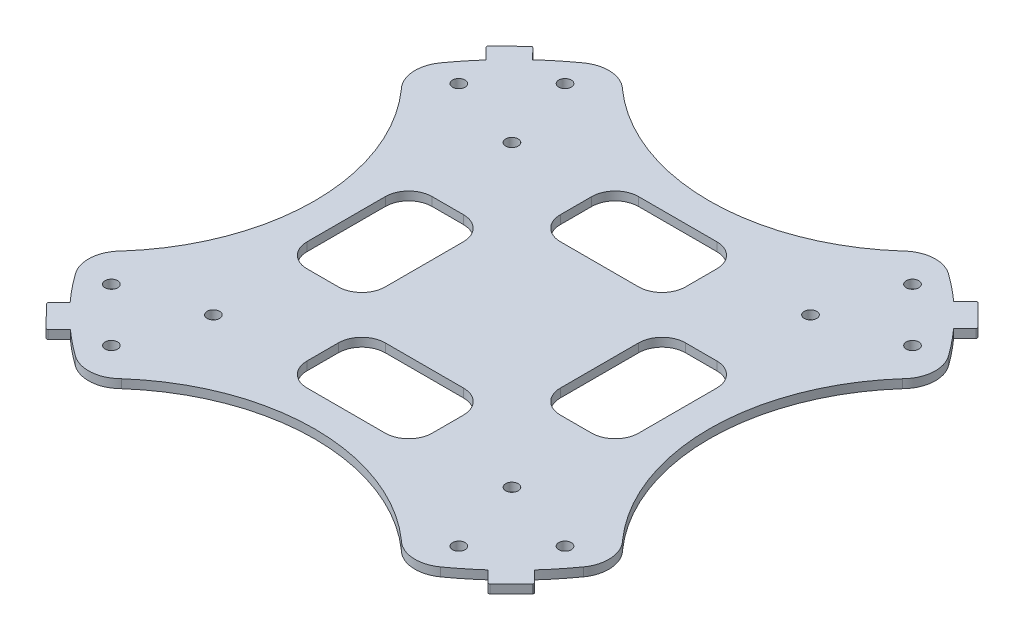
SolidWorks part; units mm, degrees
ref_plane "Front Plane" through (0, 0, 0) normal (0, 0, 1) x (1, 0, 0)
ref_plane "Top Plane" through (0, 0, 0) normal (0, 1, 0) x (1, 0, 0)
ref_plane "Right Plane" through (0, 0, 0) normal (1, 0, 0) x (0, 0, -1)
sketch "Sketch1" plane through (0, 0, 0) normal (0, 1, 0) x (1, 0, 0)
  line L0 (-1000, 0) -> (49000, 0) construction
  line L1 (0, -1000) -> (0, 49000) construction
  line L2 (707.1069, -707.1069) -> (-34648.2322, 34648.2322) construction
  line L3 (-707.1068, -707.1068) -> (34648.2323, 34648.2323) construction
  line L4 (716.0871, -698.1266) -> (0, 17.9605) construction
  line L5 (-698.1265, -716.087) -> (34657.2125, 34639.252) construction
  line L6 (698.1266, -716.0871) -> (-34657.2125, 34639.2519) construction
  line L7 (-716.087, -698.1265) -> (0, 17.9605) construction
  line L8 (-733.6258, -670.2104) -> (-31.7077, 31.7077) construction
  line L9 (733.9751, -670.5597) -> (22.7274, 40.6879) construction
  line L10 (39.5829, 36.115) -> (36.1358, 39.5583)
  line L11 (716.0871, -698.1266) -> (-34639.2519, 34657.2125) construction
  line L12 (35.7817, 39.5534) -> (33.9856, 37.7573)
  line L13 (-716.087, -698.1265) -> (34639.252, 34657.2125) construction
  line L14 (39.5739, 35.7609) -> (37.7573, 33.9856)
  line L15 (39.5382, -36.1548) -> (36.0819, -39.6111)
  line L16 (39.5078, -35.8322) -> (37.7118, -34.0362)
  line L17 (-35.9968, -39.6764) -> (-39.3444, -36.2512)
  line L18 (-37.6038, -34.1555) -> (-39.3423, -35.894)
  line L19 (35.7129, -39.6171) -> (33.9376, -37.8006)
  line L20 (-35.6141, -39.7036) -> (-33.8181, -37.9075)
  line L21 (-39.7221, 35.8999) -> (-36.251, 39.2922)
  line L22 (-34.2033, 37.5603) -> (-35.8918, 39.2881)
  line L24 (-37.9528, 33.7672) -> (-39.7242, 35.5386)
  line L30 (-39.4203, -35.9308) -> (-37.6038, -34.1555) [skipped]
  line L31 (-39.7488, 35.5633) -> (-37.9528, 33.7672) [skipped]
  line L32 (-35.9786, 39.3768) -> (-34.2033, 37.5603) [skipped]
  arc A0 (-29.6486, 41.2505) -> (-34.2033, 37.5603) centre (0, 0) ccw construction
  arc A1 (-22.7274, 40.6879) -> (-29.6486, 41.2505) centre (-26.519, 36.8963) ccw
  arc A2 (-40.6879, 22.7274) -> (-41.2505, 29.6486) centre (-36.8963, 26.519) cw
  arc A3 (22.7274, 40.6879) -> (29.6486, 41.2505) centre (26.519, 36.8963) cw
  arc A4 (40.6879, 22.7274) -> (41.2505, 29.6486) centre (36.8963, 26.519) ccw
  arc A5 (40.6879, -22.7274) -> (41.2505, -29.6486) centre (36.8963, -26.519) cw
  arc A6 (22.7274, -40.6879) -> (29.6486, -41.2505) centre (26.519, -36.8963) ccw
  arc A7 (-22.7274, -40.6879) -> (-29.6486, -41.2505) centre (-26.519, -36.8963) cw
  arc A8 (-40.6879, -22.7274) -> (-41.2505, -29.6486) centre (-36.8963, -26.519) ccw
  arc A9 (-22.7274, 40.6879) -> (22.7274, 40.6879) centre (0, 66.2866) ccw
  arc A10 (40.6879, 22.7274) -> (40.6879, -22.7274) centre (66.2866, 0) ccw
  arc A11 (22.7274, -40.6879) -> (-22.7274, -40.6879) centre (0, -66.2866) ccw
  arc A12 (-40.6879, -22.7274) -> (-40.6879, 22.7274) centre (-66.2866, 0) ccw
  arc A13 (-29.6486, 41.2505) -> (-34.2033, 37.5603) centre (0, 0) ccw
  arc A14 (41.2505, 29.6486) -> (37.7573, 33.9856) centre (0, 0) ccw construction
  arc A15 (41.2505, 29.6486) -> (37.7573, 33.9856) centre (0, 0) ccw
  arc A16 (29.6486, -41.2505) -> (33.9376, -37.8006) centre (0, 0) ccw construction
  arc A17 (29.6486, -41.2505) -> (33.9376, -37.8006) centre (0, 0) ccw
  arc A18 (-41.2505, -29.6486) -> (-37.6038, -34.1555) centre (0, 0) ccw construction
  arc A19 (-41.2505, -29.6486) -> (-37.6038, -34.1555) centre (0, 0) ccw
  arc A20 (33.9856, 37.7573) -> (29.6486, 41.2505) centre (0, 0) ccw construction
  arc A21 (33.9856, 37.7573) -> (29.6486, 41.2505) centre (0, 0) ccw
  arc A22 (37.7118, -34.0362) -> (41.2505, -29.6486) centre (0, 0) ccw construction
  arc A23 (37.7118, -34.0362) -> (41.2505, -29.6486) centre (0, 0) ccw
  arc A24 (-33.8181, -37.9075) -> (-29.6486, -41.2505) centre (0, 0) ccw construction
  arc A25 (-33.8181, -37.9075) -> (-29.6486, -41.2505) centre (0, 0) ccw
  arc A26 (-37.9528, 33.7672) -> (-41.2505, 29.6486) centre (0, 0) ccw construction
  arc A27 (-37.9528, 33.7672) -> (-41.2505, 29.6486) centre (0, 0) ccw
  arc A28 (-35.6141, -39.7036) -> (-35.9968, -39.6764) centre (-35.7937, -39.5239) cw
  arc A29 (-39.3423, -35.894) -> (-39.3444, -36.2512) centre (-39.1627, -36.0736) ccw
  arc A30 (35.7129, -39.6171) -> (36.0819, -39.6111) centre (35.8945, -39.4396) ccw
  arc A31 (39.5078, -35.8322) -> (39.5382, -36.1548) centre (39.3282, -36.0118) cw
  arc A32 (39.5739, 35.7609) -> (39.5829, 36.115) centre (39.3964, 35.9426) ccw
  arc A33 (36.1358, 39.5583) -> (35.7817, 39.5534) centre (35.9613, 39.3738) ccw
  arc A34 (-39.7221, 35.8999) -> (-39.7242, 35.5386) centre (-39.5446, 35.7182) ccw
  arc A35 (-36.251, 39.2922) -> (-35.8918, 39.2881) centre (-36.0735, 39.1105) cw
  circle A36 centre (-28.2202, 36.8412) radius 1.016
  circle A37 centre (-36.8412, 28.2202) radius 1.016
  circle A38 centre (-24.2455, 24.2455) radius 1.016
  circle A39 centre (28.2202, 36.8412) radius 1.016
  circle A40 centre (36.8412, 28.2202) radius 1.016
  circle A41 centre (24.2455, 24.2455) radius 1.016
  circle A42 centre (36.8412, -28.2202) radius 1.016
  circle A43 centre (28.2202, -36.8412) radius 1.016
  circle A44 centre (24.2455, -24.2455) radius 1.016
  circle A45 centre (-28.2202, -36.8412) radius 1.016
  circle A46 centre (-36.8412, -28.2202) radius 1.016
  circle A47 centre (-24.2455, -24.2455) radius 1.016
  point P46 (0, 0)
  point P60 (0, 0)
  point P75 (-0.048, -0.2069)
  point P83 (41.6473, 37.8756)
  point P86 (37.8756, 41.6473)
  point P120 (0, 0)
  dimension "D1" = 12.7
  dimension "D3" = 4
  dimension "D4" = 4
  dimension "D7" = 0.254
  dimension "D8" = 50.8
  dimension "D10" = 0.254
  dimension "D9" = 0.254
  dimension "D13" = 13.208
  dimension "D5" = 2.667
  dimension "D11" = 12.192
  dimension "D12" = 7.366
  dimension "D2" = 12.7
  dimension "D6" = 4
  dimension "D14" = 4
extrude "Boss-Extrude1" add sketch "Sketch1" along normal blind 1.397
sketch "Sketch3" plane through (0, 1.397, 0) normal (0, 1, 0) x (1, 0, 0)
  line L0 (0, 0) -> (0, 50000) construction
  line L1 (26.924, 6.35) -> (26.924, -6.35)
  line L2 (-6.35, 26.924) -> (6.35, 26.924)
  line L3 (-10.16, 23.114) -> (-10.16, 18.034)
  line L4 (-6.35, 14.224) -> (6.35, 14.224)
  line L5 (10.16, 23.114) -> (10.16, 18.034)
  line L6 (-10.16, 26.924) -> (10.16, 14.224) construction
  line L7 (-10.16, 14.224) -> (10.16, 26.924) construction
  line L8 (23.114, -10.16) -> (18.034, -10.16)
  line L9 (14.224, 6.35) -> (14.224, -6.35)
  line L10 (23.114, 10.16) -> (18.034, 10.16)
  line L11 (6.35, -26.924) -> (-6.35, -26.924)
  line L12 (-10.16, -23.114) -> (-10.16, -18.034)
  line L13 (6.35, -14.224) -> (-6.35, -14.224)
  line L14 (10.16, -23.114) -> (10.16, -18.034)
  line L15 (-26.924, -6.35) -> (-26.924, 6.35)
  line L16 (-23.114, 10.16) -> (-18.034, 10.16)
  line L17 (-14.224, -6.35) -> (-14.224, 6.35)
  line L18 (-23.114, -10.16) -> (-18.034, -10.16)
  arc A0 (-10.16, 23.114) -> (-6.35, 26.924) centre (-6.35, 23.114) cw
  arc A1 (-10.16, 18.034) -> (-6.35, 14.224) centre (-6.35, 18.034) ccw
  arc A2 (10.16, 18.034) -> (6.35, 14.224) centre (6.35, 18.034) cw
  arc A3 (10.16, 23.114) -> (6.35, 26.924) centre (6.35, 23.114) ccw
  arc A4 (23.114, 10.16) -> (26.924, 6.35) centre (23.114, 6.35) cw
  arc A5 (23.114, -10.16) -> (26.924, -6.35) centre (23.114, -6.35) ccw
  arc A6 (18.034, 10.16) -> (14.224, 6.35) centre (18.034, 6.35) ccw
  arc A7 (18.034, -10.16) -> (14.224, -6.35) centre (18.034, -6.35) cw
  arc A8 (10.16, -23.114) -> (6.35, -26.924) centre (6.35, -23.114) cw
  arc A9 (-10.16, -23.114) -> (-6.35, -26.924) centre (-6.35, -23.114) ccw
  arc A10 (10.16, -18.034) -> (6.35, -14.224) centre (6.35, -18.034) ccw
  arc A11 (-10.16, -18.034) -> (-6.35, -14.224) centre (-6.35, -18.034) cw
  arc A12 (-23.114, -10.16) -> (-26.924, -6.35) centre (-23.114, -6.35) cw
  arc A13 (-23.114, 10.16) -> (-26.924, 6.35) centre (-23.114, 6.35) ccw
  arc A14 (-18.034, -10.16) -> (-14.224, -6.35) centre (-18.034, -6.35) ccw
  arc A15 (-18.034, 10.16) -> (-14.224, 6.35) centre (-18.034, 6.35) cw
  point P3 (0, 20.574)
  point P59 (0, 0)
  dimension "D3" = 26.924
  dimension "D4" = 3.81
  dimension "D1" = 12.7
  dimension "D2" = 20.32
  dimension "D5" = 4
extrude "Cut-Extrude1" cut sketch "Sketch3" against normal blind 1.397
sketch "Sketch4" plane through (0, 0, 0) normal (0, -1, 0) x (1, 0, 0)
  line L24 (34.0319, -34.9752) -> (35.9619, -36.9052)
  line L25 (35.9619, -36.9052) -> (36.9121, -35.956)
  line L26 (36.9121, -35.956) -> (34.9596, -34.048)
  line L27 (34.9278, 34.0806) -> (36.8559, 36.0087)
  line L28 (36.8559, 36.0087) -> (35.9086, 36.9559)
  line L29 (35.9086, 36.9559) -> (34.0017, 35.0047)
  line L30 (-33.8705, 35.1316) -> (-35.778, 37.039)
  line L31 (-35.778, 37.039) -> (-36.7076, 36.0877)
  line L32 (-36.7076, 36.0877) -> (-34.8154, 34.1955)
  line L33 (-35.1787, -33.8216) -> (-37.0611, -35.704)
  line L34 (-37.0611, -35.704) -> (-36.1018, -36.6415)
  line L35 (-36.1018, -36.6415) -> (-34.2575, -34.7543)
  line L36 (34.0319, -34.9752) -> (35.9619, -36.9052)
  line L37 (35.9619, -36.9052) -> (36.9121, -35.956)
  line L38 (36.9121, -35.956) -> (34.9596, -34.048)
  line L39 (34.9278, 34.0806) -> (36.8559, 36.0087)
  line L40 (36.8559, 36.0087) -> (35.9086, 36.9559)
  line L41 (35.9086, 36.9559) -> (34.0017, 35.0047)
  line L42 (-33.8705, 35.1316) -> (-35.778, 37.039)
  line L43 (-35.778, 37.039) -> (-36.7076, 36.0877)
  line L44 (-36.7076, 36.0877) -> (-34.8154, 34.1955)
  line L45 (-35.1787, -33.8216) -> (-37.0611, -35.704)
  line L46 (-37.0611, -35.704) -> (-36.1018, -36.6415)
  line L47 (-36.1018, -36.6415) -> (-34.2575, -34.7543)
  line L60 (33.9856, -37.7573) -> (35.7817, -39.5534)
  line L61 (36.1358, -39.5583) -> (39.5829, -36.115)
  line L62 (39.5739, -35.7609) -> (37.7573, -33.9856)
  line L63 (37.7118, 34.0362) -> (39.5078, 35.8322)
  line L64 (39.5382, 36.1548) -> (36.0819, 39.6111)
  line L65 (35.7129, 39.6171) -> (33.9376, 37.8006)
  line L66 (-33.8181, 37.9075) -> (-35.6141, 39.7036)
  line L67 (-35.9968, 39.6764) -> (-39.3444, 36.2512)
  line L68 (-39.3423, 35.894) -> (-37.6038, 34.1555)
  line L69 (-37.9528, -33.7672) -> (-39.7242, -35.5386)
  line L70 (-39.7221, -35.8999) -> (-36.251, -39.2922)
  line L71 (-35.8918, -39.2881) -> (-34.2033, -37.5603)
  line L72 (33.9856, -37.7573) -> (35.7817, -39.5534)
  line L73 (36.1358, -39.5583) -> (39.5829, -36.115)
  line L74 (39.5739, -35.7609) -> (37.7573, -33.9856)
  line L75 (37.7118, 34.0362) -> (39.5078, 35.8322)
  line L76 (39.5382, 36.1548) -> (36.0819, 39.6111)
  line L77 (35.7129, 39.6171) -> (33.9376, 37.8006)
  line L78 (-33.8181, 37.9075) -> (-35.6141, 39.7036)
  line L79 (-35.9968, 39.6764) -> (-39.3444, 36.2512)
  line L80 (-39.3423, 35.894) -> (-37.6038, 34.1555)
  line L81 (-37.9528, -33.7672) -> (-39.7242, -35.5386)
  line L82 (-39.7221, -35.8999) -> (-36.251, -39.2922)
  line L83 (-35.8918, -39.2881) -> (-34.2033, -37.5603)
  arc A56 (-34.2575, -34.7543) -> (-28.4813, -39.6265) centre (0, 0) ccw
  arc A57 (-28.4813, -39.6265) -> (-24.1054, -39.2369) centre (-26.519, -36.8963) ccw
  arc A58 (24.1054, -39.2369) -> (-24.1054, -39.2369) centre (0, -66.2866) ccw
  arc A59 (24.1054, -39.2369) -> (28.4813, -39.6265) centre (26.519, -36.8963) ccw
  arc A60 (28.4813, -39.6265) -> (34.0319, -34.9752) centre (0, 0) ccw
  arc A61 (34.9596, -34.048) -> (39.6265, -28.4813) centre (0, 0) ccw
  arc A62 (39.6265, -28.4813) -> (39.2369, -24.1054) centre (36.8963, -26.519) ccw
  arc A63 (39.2369, 24.1054) -> (39.2369, -24.1054) centre (66.2866, 0) ccw
  arc A64 (39.2369, 24.1054) -> (39.6265, 28.4813) centre (36.8963, 26.519) ccw
  arc A65 (39.6265, 28.4813) -> (34.9278, 34.0806) centre (0, 0) ccw
  arc A66 (34.0017, 35.0047) -> (28.4813, 39.6265) centre (0, 0) ccw
  arc A67 (28.4813, 39.6265) -> (24.1054, 39.2369) centre (26.519, 36.8963) ccw
  arc A68 (-24.1054, 39.2369) -> (24.1054, 39.2369) centre (0, 66.2866) ccw
  arc A69 (-24.1054, 39.2369) -> (-28.4813, 39.6265) centre (-26.519, 36.8963) ccw
  arc A70 (-28.4813, 39.6265) -> (-33.8705, 35.1316) centre (0, 0) ccw
  arc A71 (-34.8154, 34.1955) -> (-39.6265, 28.4813) centre (0, 0) ccw
  arc A72 (-39.6265, 28.4813) -> (-39.2369, 24.1054) centre (-36.8963, 26.519) ccw
  arc A73 (-39.2369, -24.1054) -> (-39.2369, 24.1054) centre (-66.2866, 0) ccw
  arc A74 (-39.2369, -24.1054) -> (-39.6265, -28.4813) centre (-36.8963, -26.519) ccw
  arc A75 (-39.6265, -28.4813) -> (-35.1787, -33.8216) centre (0, 0) ccw
  arc A76 (-34.2575, -34.7543) -> (-28.4813, -39.6265) centre (0, 0) ccw
  arc A77 (-28.4813, -39.6265) -> (-24.1054, -39.2369) centre (-26.519, -36.8963) ccw
  arc A78 (24.1054, -39.2369) -> (-24.1054, -39.2369) centre (0, -66.2866) ccw
  arc A79 (24.1054, -39.2369) -> (28.4813, -39.6265) centre (26.519, -36.8963) ccw
  arc A80 (28.4813, -39.6265) -> (34.0319, -34.9752) centre (0, 0) ccw
  arc A81 (34.9596, -34.048) -> (39.6265, -28.4813) centre (0, 0) ccw
  arc A82 (39.6265, -28.4813) -> (39.2369, -24.1054) centre (36.8963, -26.519) ccw
  arc A83 (39.2369, 24.1054) -> (39.2369, -24.1054) centre (66.2866, 0) ccw
  arc A84 (39.2369, 24.1054) -> (39.6265, 28.4813) centre (36.8963, 26.519) ccw
  arc A85 (39.6265, 28.4813) -> (34.9278, 34.0806) centre (0, 0) ccw
  arc A86 (34.0017, 35.0047) -> (28.4813, 39.6265) centre (0, 0) ccw
  arc A87 (28.4813, 39.6265) -> (24.1054, 39.2369) centre (26.519, 36.8963) ccw
  arc A88 (-24.1054, 39.2369) -> (24.1054, 39.2369) centre (0, 66.2866) ccw
  arc A89 (-24.1054, 39.2369) -> (-28.4813, 39.6265) centre (-26.519, 36.8963) ccw
  arc A90 (-28.4813, 39.6265) -> (-33.8705, 35.1316) centre (0, 0) ccw
  arc A91 (-34.8154, 34.1955) -> (-39.6265, 28.4813) centre (0, 0) ccw
  arc A92 (-39.6265, 28.4813) -> (-39.2369, 24.1054) centre (-36.8963, 26.519) ccw
  arc A93 (-39.2369, -24.1054) -> (-39.2369, 24.1054) centre (-66.2866, 0) ccw
  arc A94 (-39.2369, -24.1054) -> (-39.6265, -28.4813) centre (-36.8963, -26.519) ccw
  arc A95 (-39.6265, -28.4813) -> (-35.1787, -33.8216) centre (0, 0) ccw
  arc A124 (-34.2033, -37.5603) -> (-29.6486, -41.2505) centre (0, 0) ccw
  arc A125 (-29.6486, -41.2505) -> (-22.7274, -40.6879) centre (-26.519, -36.8963) ccw
  arc A126 (22.7274, -40.6879) -> (-22.7274, -40.6879) centre (0, -66.2866) ccw
  arc A127 (22.7274, -40.6879) -> (29.6486, -41.2505) centre (26.519, -36.8963) ccw
  arc A128 (29.6486, -41.2505) -> (33.9856, -37.7573) centre (0, 0) ccw
  arc A129 (35.7817, -39.5534) -> (36.1358, -39.5583) centre (35.9613, -39.3738) ccw
  arc A130 (39.5829, -36.115) -> (39.5739, -35.7609) centre (39.3964, -35.9426) ccw
  arc A131 (37.7573, -33.9856) -> (41.2505, -29.6486) centre (0, 0) ccw
  arc A132 (41.2505, -29.6486) -> (40.6879, -22.7274) centre (36.8963, -26.519) ccw
  arc A133 (40.6879, 22.7274) -> (40.6879, -22.7274) centre (66.2866, 0) ccw
  arc A134 (40.6879, 22.7274) -> (41.2505, 29.6486) centre (36.8963, 26.519) ccw
  arc A135 (41.2505, 29.6486) -> (37.7118, 34.0362) centre (0, 0) ccw
  arc A136 (39.5078, 35.8322) -> (39.5382, 36.1548) centre (39.3282, 36.0118) ccw
  arc A137 (36.0819, 39.6111) -> (35.7129, 39.6171) centre (35.8945, 39.4396) ccw
  arc A138 (33.9376, 37.8006) -> (29.6486, 41.2505) centre (0, 0) ccw
  arc A139 (29.6486, 41.2505) -> (22.7274, 40.6879) centre (26.519, 36.8963) ccw
  arc A140 (-22.7274, 40.6879) -> (22.7274, 40.6879) centre (0, 66.2866) ccw
  arc A141 (-22.7274, 40.6879) -> (-29.6486, 41.2505) centre (-26.519, 36.8963) ccw
  arc A142 (-29.6486, 41.2505) -> (-33.8181, 37.9075) centre (0, 0) ccw
  arc A143 (-35.6141, 39.7036) -> (-35.9968, 39.6764) centre (-35.7937, 39.5239) ccw
  arc A144 (-39.3444, 36.2512) -> (-39.3423, 35.894) centre (-39.1627, 36.0736) ccw
  arc A145 (-37.6038, 34.1555) -> (-41.2505, 29.6486) centre (0, 0) ccw
  arc A146 (-41.2505, 29.6486) -> (-40.6879, 22.7274) centre (-36.8963, 26.519) ccw
  arc A147 (-40.6879, -22.7274) -> (-40.6879, 22.7274) centre (-66.2866, 0) ccw
  arc A148 (-40.6879, -22.7274) -> (-41.2505, -29.6486) centre (-36.8963, -26.519) ccw
  arc A149 (-41.2505, -29.6486) -> (-37.9528, -33.7672) centre (0, 0) ccw
  arc A150 (-39.7242, -35.5386) -> (-39.7221, -35.8999) centre (-39.5446, -35.7182) ccw
  arc A151 (-36.251, -39.2922) -> (-35.8918, -39.2881) centre (-36.0735, -39.1105) ccw
  arc A152 (-34.2033, -37.5603) -> (-29.6486, -41.2505) centre (0, 0) ccw
  arc A153 (-29.6486, -41.2505) -> (-22.7274, -40.6879) centre (-26.519, -36.8963) ccw
  arc A154 (22.7274, -40.6879) -> (-22.7274, -40.6879) centre (0, -66.2866) ccw
  arc A155 (22.7274, -40.6879) -> (29.6486, -41.2505) centre (26.519, -36.8963) ccw
  arc A156 (29.6486, -41.2505) -> (33.9856, -37.7573) centre (0, 0) ccw
  arc A157 (35.7817, -39.5534) -> (36.1358, -39.5583) centre (35.9613, -39.3738) ccw
  arc A158 (39.5829, -36.115) -> (39.5739, -35.7609) centre (39.3964, -35.9426) ccw
  arc A159 (37.7573, -33.9856) -> (41.2505, -29.6486) centre (0, 0) ccw
  arc A160 (41.2505, -29.6486) -> (40.6879, -22.7274) centre (36.8963, -26.519) ccw
  arc A161 (40.6879, 22.7274) -> (40.6879, -22.7274) centre (66.2866, 0) ccw
  arc A162 (40.6879, 22.7274) -> (41.2505, 29.6486) centre (36.8963, 26.519) ccw
  arc A163 (41.2505, 29.6486) -> (37.7118, 34.0362) centre (0, 0) ccw
  arc A164 (39.5078, 35.8322) -> (39.5382, 36.1548) centre (39.3282, 36.0118) ccw
  arc A165 (36.0819, 39.6111) -> (35.7129, 39.6171) centre (35.8945, 39.4396) ccw
  arc A166 (33.9376, 37.8006) -> (29.6486, 41.2505) centre (0, 0) ccw
  arc A167 (29.6486, 41.2505) -> (22.7274, 40.6879) centre (26.519, 36.8963) ccw
  arc A168 (-22.7274, 40.6879) -> (22.7274, 40.6879) centre (0, 66.2866) ccw
  arc A169 (-22.7274, 40.6879) -> (-29.6486, 41.2505) centre (-26.519, 36.8963) ccw
  arc A170 (-29.6486, 41.2505) -> (-33.8181, 37.9075) centre (0, 0) ccw
  arc A171 (-35.6141, 39.7036) -> (-35.9968, 39.6764) centre (-35.7937, 39.5239) ccw
  arc A172 (-39.3444, 36.2512) -> (-39.3423, 35.894) centre (-39.1627, 36.0736) ccw
  arc A173 (-37.6038, 34.1555) -> (-41.2505, 29.6486) centre (0, 0) ccw
  arc A174 (-41.2505, 29.6486) -> (-40.6879, 22.7274) centre (-36.8963, 26.519) ccw
  arc A175 (-40.6879, -22.7274) -> (-40.6879, 22.7274) centre (-66.2866, 0) ccw
  arc A176 (-40.6879, -22.7274) -> (-41.2505, -29.6486) centre (-36.8963, -26.519) ccw
  arc A177 (-41.2505, -29.6486) -> (-37.9528, -33.7672) centre (0, 0) ccw
  arc A178 (-39.7242, -35.5386) -> (-39.7221, -35.8999) centre (-39.5446, -35.7182) ccw
  arc A179 (-36.251, -39.2922) -> (-35.8918, -39.2881) centre (-36.0735, -39.1105) ccw
  dimension "D1" = 2
  dimension "D2" = 0
extrude "Boss-Extrude2" add sketch "Sketch4" along normal blind 0.01
